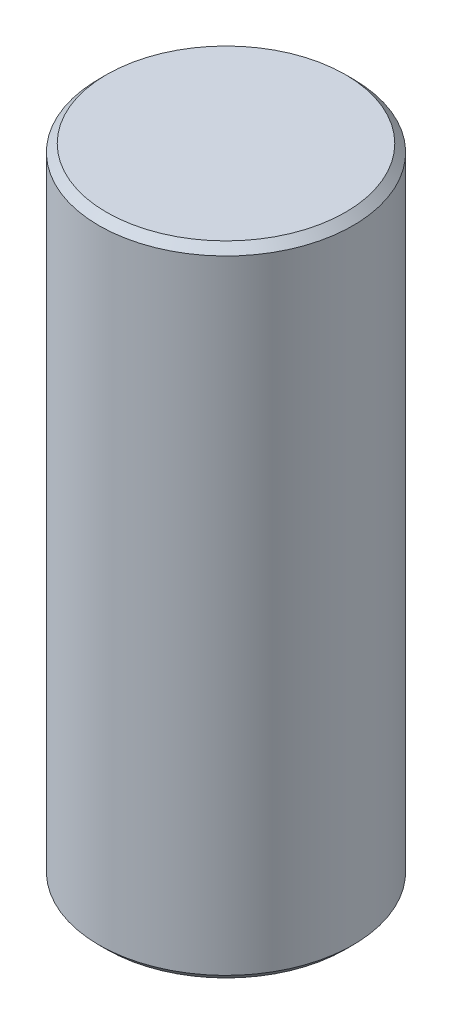
SolidWorks part; units mm, degrees
material "Brass"
ref_plane "Front" through (0, 0, 0) normal (0, 0, 1) x (1, 0, 0)
ref_plane "Top" through (0, 0, 0) normal (0, 1, 0) x (1, 0, 0)
ref_plane "Right" through (0, 0, 0) normal (1, 0, 0) x (0, 0, -1)
sketch "Sketch1" plane through (0, 0, 0) normal (0, 0, 1) x (1, 0, 0)
  line L0 (12.6365, 0.762) -> (12.6365, 62.738)
  line L1 (11.8745, 0) -> (6.3754, 0)
  line L2 (6.3754, 0) -> (6.3754, 4.572)
  line L3 (6.1214, 4.826) -> (0, 4.826)
  line L6 (0, 4.826) -> (0, 63.5)
  line L7 (11.8745, 63.5) -> (0, 63.5)
  line L8 (0, 0) -> (6.3754, 0) construction
  line L9 (0, 0) -> (0, 4.826) construction
  line L10 (6.3754, 4.572) -> (6.1214, 4.826)
  line L12 (12.6365, 62.738) -> (11.8745, 63.5)
  line L13 (12.6365, 0.762) -> (11.8745, 0)
  point P0 (12.6365, 0)
  point P1 (12.6365, 63.5)
  point P4 (6.3754, 4.826)
  dimension "D1" = 63.5
  dimension "D2" = 4.826
  dimension "D5" = 12.7508
  dimension "D6" = 25.273
  dimension "D9" = 0.254
  dimension "D11" = 0.762
  dimension "D12" = 0.762
revolve "Revolve1" add sketch "Sketch1" angle 360 about L9
